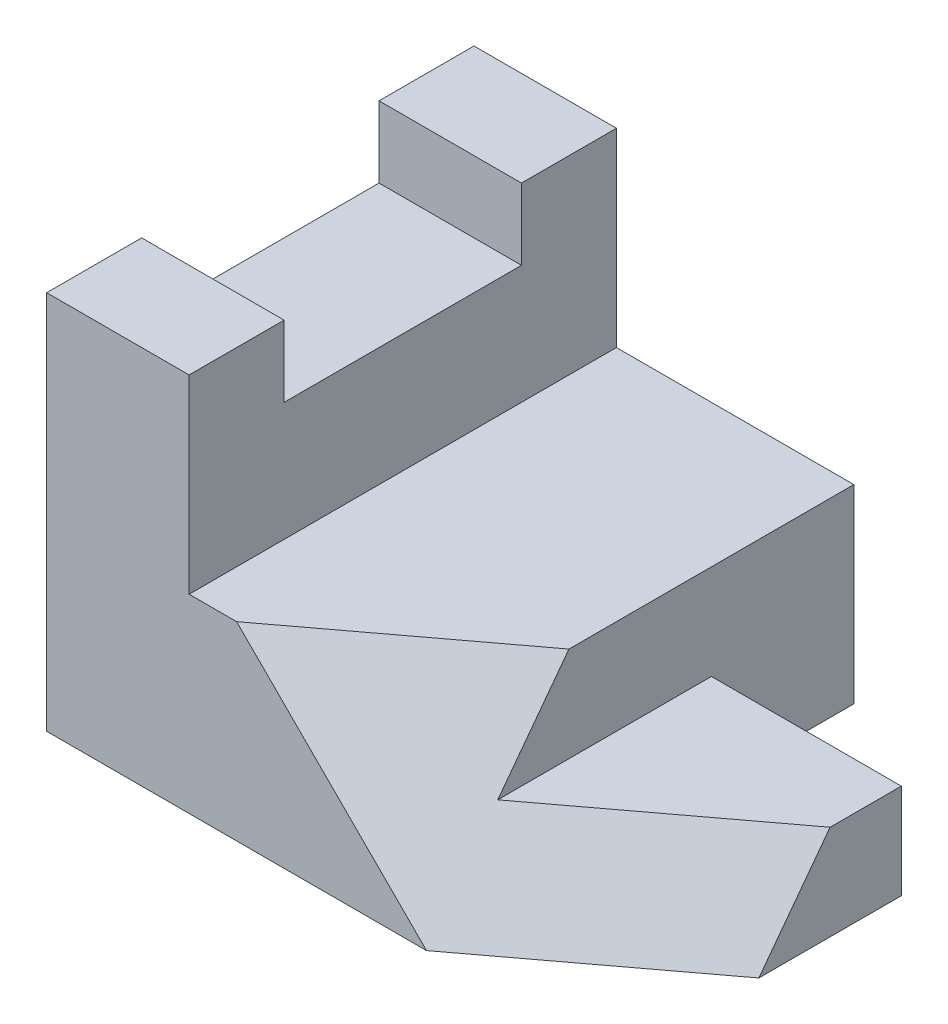
SolidWorks part; units mm, degrees
ref_plane "Front Plane" through (0, 0, 0) normal (0, 0, 1) x (1, 0, 0)
ref_plane "Top Plane" through (0, 0, 0) normal (0, 1, 0) x (1, 0, 0)
ref_plane "Right Plane" through (0, 0, 0) normal (1, 0, 0) x (0, 0, -1)
sketch "Sketch1" plane through (0, 0, 0) normal (1, 0, 0) x (0, 0, -1)
  line L1 (-57.15, 0) -> (0, 0)
  line L2 (-57.15, 0) -> (-57.15, 25.4)
  line L3 (-57.15, 25.4) -> (0, 25.4)
  line L4 (0, 0) -> (0, 25.4)
  dimension "D1" = 57.15
  dimension "D2" = 25.4
extrude "Boss-Extrude1" add sketch "Sketch1" against normal blind 57.15
sketch "Sketch2" plane through (0, 25.4, 0) normal (0, 1, 0) x (1, 0, 0)
  line L1 (0, 0) -> (-25.4, 0)
  line L2 (0, 0) -> (0, -19.05)
  line L3 (0, -19.05) -> (-25.4, -19.05)
  line L4 (-25.4, 0) -> (-25.4, -19.05)
  dimension "D1" = 19.05
  dimension "D2" = 25.4
extrude "Cut-Extrude1" cut sketch "Sketch2" against normal through all
sketch "Sketch3" plane through (0, 0, 0) normal (1, 0, 0) x (0, 0, -1)
  line L0 (-38.1, 0) -> (-19.05, 25.4) construction
  line L1 (-57.15, 0) -> (-19.05, 0) construction
  dimension "D1" = 19.05
sketch "Sketch4" plane through (0, 0, 57.15) normal (0, 0, 1) x (1, 0, 0)
  line L0 (-25.4, 0) -> (-50.8, 25.4) construction
  line L1 (-57.15, 0) -> (0, 0) construction
  line L2 (-57.15, 25.4) -> (0, 25.4) construction
  dimension "D1" = 6.35
  dimension "D2" = 31.75
ref_plane "Plane1" through (13.4471, 13.4471, 17.9294) normal (0.5145, 0.5145, 0.686) x (0.8575, -0.3087, -0.4116)
other "SurfaceCut1"
sketch "Sketch5" plane through (0, 0, 19.05) normal (0, 0, -1) x (-1, 0, 0)
  line L0 (25.4, 0) -> (25.4, 25.4) construction
  line L1 (0, 25.4) -> (25.4, 25.4)
  line L2 (0, 25.4) -> (0, 12.7)
  line L3 (0, 12.7) -> (25.4, 12.7)
  line L4 (25.4, 25.4) -> (25.4, 12.7)
  dimension "D1" = 12.7
extrude "Cut-Extrude2" cut sketch "Sketch5" against normal through all
sketch "Sketch6" plane through (-57.15, 0, 0) normal (-1, 0, 0) x (0, 0, 1)
  line L0 (0, 0) -> (0, 50.8)
  line L1 (0, 50.8) -> (12.7, 50.8)
  line L2 (12.7, 50.8) -> (12.7, 41.275)
  line L3 (0, 25.4) -> (57.15, 25.4) construction
  line L4 (12.7, 41.275) -> (44.45, 41.275)
  line L5 (28.575, 25.4) -> (28.575, 0) construction
  line L6 (57.15, 0) -> (0, 0) construction
  line L7 (0, 0) -> (57.15, 0)
  line L8 (44.45, 50.8) -> (44.45, 41.275)
  line L9 (57.15, 50.8) -> (44.45, 50.8)
  line L10 (57.15, 0) -> (57.15, 50.8)
  point P14 (28.575, 41.275)
  dimension "D1" = 28.575
  dimension "D2" = 9.525
  dimension "D3" = 50.8
  dimension "D4" = 15.875
extrude "Boss-Extrude2" add sketch "Sketch6" along normal blind 19.05
